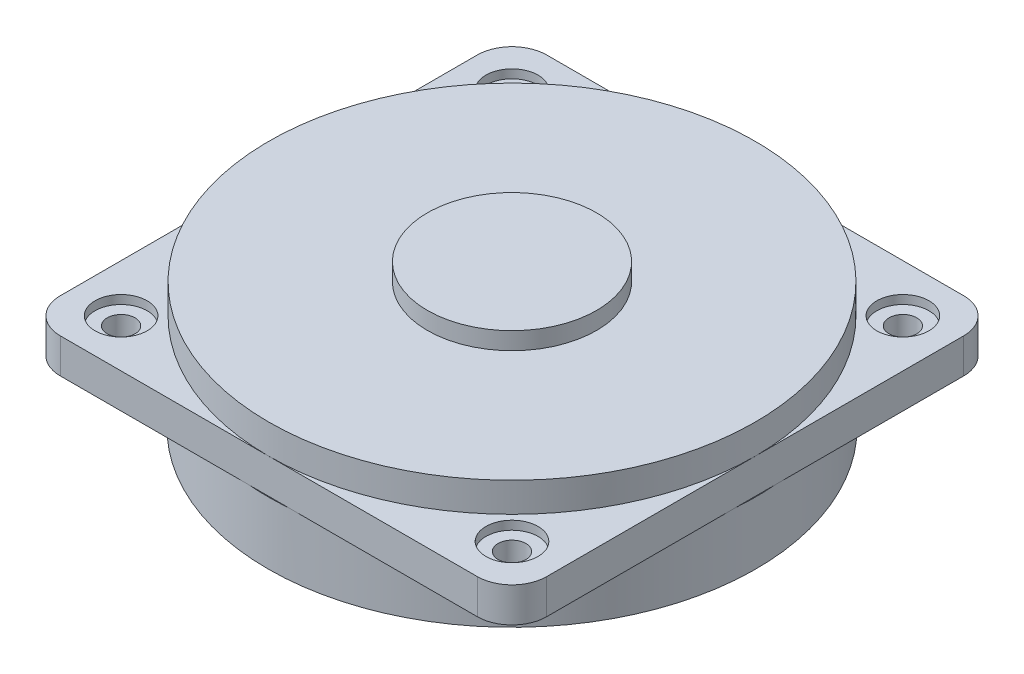
SolidWorks part; units mm, degrees
ref_plane "Front Plane" through (0, 0, 0) normal (0, 0, 1) x (1, 0, 0)
ref_plane "Top Plane" through (0, 0, 0) normal (0, 1, 0) x (1, 0, 0)
ref_plane "Right Plane" through (0, 0, 0) normal (1, 0, 0) x (0, 0, -1)
sketch "Sketch1" plane through (0, 0, 0) normal (0, 1, 0) x (1, 0, 0)
  line L1 (-14, 14) -> (14, 14)
  line L2 (-14, 14) -> (-14, -14)
  line L3 (-14, -14) -> (14, -14)
  line L4 (14, 14) -> (14, -14)
  line L5 (-14, 14) -> (14, -14) construction
  line L6 (-14, -14) -> (14, 14) construction
  point P0 (0, 0)
  dimension "D1" = 28
  dimension "D2" = 28
extrude "Boss-Extrude1" add sketch "Sketch1" along normal blind 2
sketch "Sketch2" plane through (0, 0, 0) normal (0, -1, 0) x (1, 0, 0)
  circle A0 centre (0, 0) radius 14.045
  circle A1 centre (0, 0) radius 12.545
  dimension "D1" = 28.09
  dimension "D2" = 25.09
extrude "Boss-Extrude2" add sketch "Sketch2" along normal offset from surface (3.6 mm away) 5.6 up to face at (0, 2, 0)
sketch "Sketch3" plane through (0, 2, 0) normal (0, 1, 0) x (1, 0, 0)
  line L0 (14, -14) -> (14, 14) construction
  circle A0 centre (0, 0) radius 14
extrude "Boss-Extrude3" add sketch "Sketch3" along normal offset from surface (1.7 mm away) 7.3 up to face at (0, -3.6, 12.545)
sketch "Sketch4" plane through (0, 3.7, 0) normal (0, 1, 0) x (1, 0, 0)
  circle A0 centre (0, 0) radius 4.8695
extrude "Boss-Extrude4" add sketch "Sketch4" along normal blind 1
sketch "Sketch5" plane through (0, 0, 0) normal (0, -1, 0) x (1, 0, 0)
  circle A0 centre (0, 0) radius 7.5692
extrude "Boss-Extrude5" add sketch "Sketch5" along normal up to surface (3.6 mm away) up to face at (0, -3.6, 12.545)
sketch "Sketch6" plane through (0, 2, 0) normal (0, 1, 0) x (1, 0, 0)
  line L1 (-11.25, -11.25) -> (11.25, -11.25) construction
  line L2 (-11.25, -11.25) -> (-11.25, 11.25) construction
  line L3 (-11.25, 11.25) -> (11.25, 11.25) construction
  line L4 (11.25, -11.25) -> (11.25, 11.25) construction
  line L5 (-11.25, -11.25) -> (11.25, 11.25) construction
  line L6 (-11.25, 11.25) -> (11.25, -11.25) construction
  circle A0 centre (11.25, 11.25) radius 1.5
  circle A1 centre (-11.25, 11.25) radius 1.5
  circle A2 centre (-11.25, -11.25) radius 1.5
  circle A3 centre (11.25, -11.25) radius 1.5
  point P0 (0, 0)
  dimension "D3" = 3
  dimension "D1" = 22.5
  dimension "D2" = 22.5
extrude "Cut-Extrude1" cut sketch "Sketch6" against normal blind 0.5
sketch "Sketch7" plane through (0, 1.5, 0) normal (0, 1, 0) x (1, 0, 0)
  circle A0 centre (-11.25, 11.25) radius 0.8
  circle A1 centre (11.25, 11.25) radius 0.8
  circle A2 centre (11.25, -11.25) radius 0.8
  circle A3 centre (-11.25, -11.25) radius 0.8
  dimension "D1" = 1.6
extrude "Cut-Extrude2" cut sketch "Sketch7" against normal through all
fillet "Fillet1" radius 2 4 edges at (-14, 1, 14) (14, 1, 14) (-14, 1, -14) (14, 1, -14)
